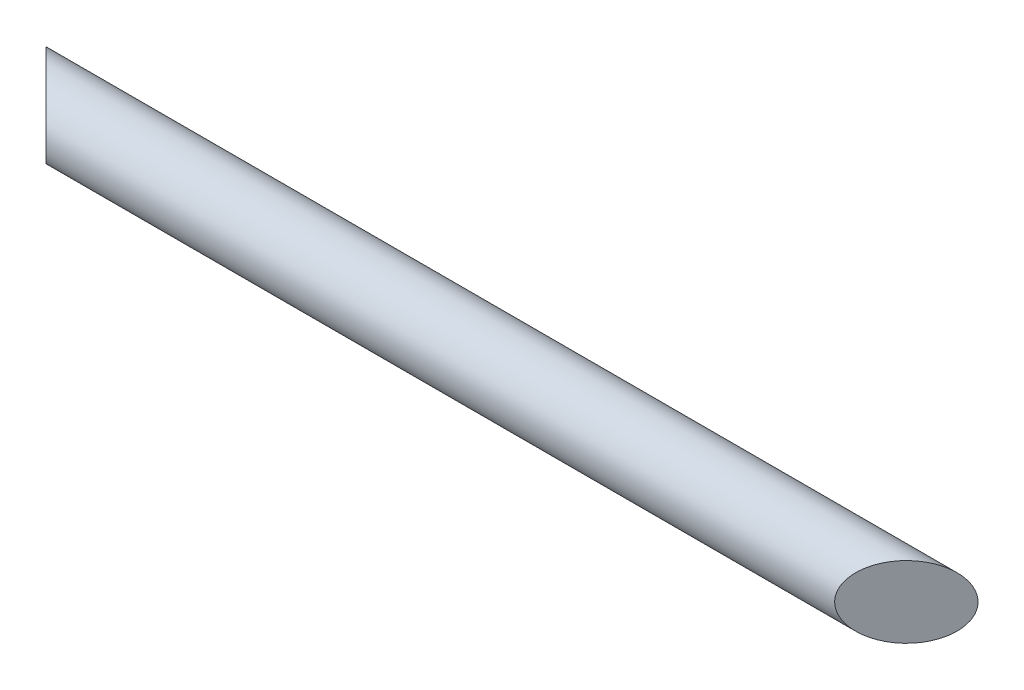
SolidWorks part; units mm, degrees
ref_plane "Front Plane" through (0, 0, 0) normal (0, 0, 1) x (1, 0, 0)
ref_plane "Top Plane" through (0, 0, 0) normal (0, 1, 0) x (1, 0, 0)
ref_plane "Right Plane" through (0, 0, 0) normal (1, 0, 0) x (0, 0, -1)
sketch "Sketch1" plane through (0, 0, 0) normal (1, 0, 0) x (0, 0, -1)
  circle A0 centre (0, 0) radius 31.75
  dimension "D1" = 63.5
extrude "Boss-Extrude1" add sketch "Sketch1" along normal blind 698.5
ref_plane "Plane1" through (0, 31.75, 0) normal (0, 1, 0) x (1, 0, 0)
sketch "Sketch5" plane through (0, 0, 0) normal (-1, 0, 0) x (0, 0, 1)
  circle A0 centre (0, 0) radius 31.75
extrude "Boss-Extrude2" add sketch "Sketch5" along normal blind 63.5
sketch "Sketch6" plane through (698.5, 0, 0) normal (1, 0, 0) x (0, 0, -1)
  circle A0 centre (0, 0) radius 31.75
extrude "Boss-Extrude3" add sketch "Sketch6" along normal blind 63.5
sketch "Sketch7" plane through (0, 31.75, 0) normal (0, 1, 0) x (1, 0, 0)
  line L0 (0, 0) -> (0, 31.75)
  line L1 (0, -31.75) -> (0, 31.75) construction
  line L2 (0, 0) -> (0, -31.75)
  line L3 (0, -31.75) -> (-63.5, -31.75)
  line L4 (-63.5, -31.75) -> (-63.5, 31.75)
  line L5 (-63.5, 31.75) -> (-63.5, -31.75) construction
  line L6 (-63.5, 31.75) -> (0, 31.75)
  line L7 (0, -31.75) -> (-63.5, 31.75)
  line L8 (698.5, 0) -> (698.5, -31.75)
  line L9 (698.5, -31.75) -> (698.5, 31.75) construction
  line L10 (-63.5, -31.75) -> (762, -31.75) construction
  line L11 (698.5, -31.75) -> (762, -31.75)
  line L12 (762, -31.75) -> (762, 31.75)
  line L13 (762, 31.75) -> (698.5, 31.75)
  line L14 (762, 31.75) -> (-63.5, 31.75) construction
  line L15 (698.5, 31.75) -> (698.5, 0)
  line L16 (698.5, -31.75) -> (762, 31.75)
extrude "Cut-Extrude1" cut sketch "Sketch7" against normal blind 63.5 contours L3 L7 L4 | L16 L11 L12
equation "\"LengthOfBackNoodle\"= \"Length Desired@Drivetrain.SLDASM\" + 1.5"
equation "\"D1@Boss-Extrude1\"=\"LengthOfBackNoodle\""
